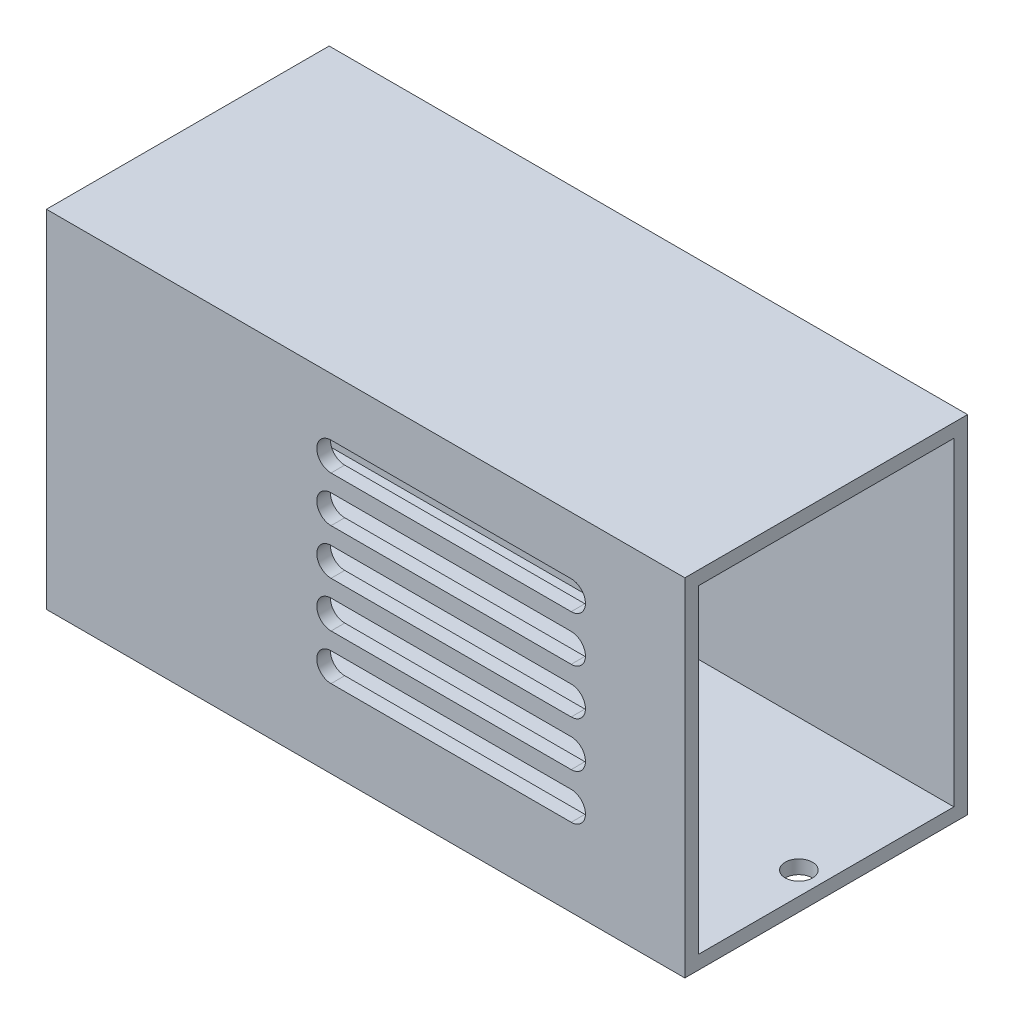
SolidWorks part; units mm, degrees
ref_plane "前视基准面" through (0, 0, 0) normal (0, 0, 1) x (1, 0, 0)
ref_plane "上视基准面" through (0, 0, 0) normal (0, 1, 0) x (1, 0, 0)
ref_plane "右视基准面" through (0, 0, 0) normal (1, 0, 0) x (0, 0, -1)
sketch "草图1" plane through (0, 0, 0) normal (0, 0, 1) x (1, 0, 0)
  line L1 (-35, 19) -> (35, 19)
  line L2 (-35, 19) -> (-35, -19)
  line L3 (-35, -19) -> (35, -19)
  line L4 (35, 19) -> (35, -19)
  line L5 (-35, 19) -> (35, -19) construction
  line L6 (-35, -19) -> (35, 19) construction
  point P0 (0, 0)
  dimension "D1" = 70
  dimension "D2" = 38
extrude "凸台-拉伸1" add sketch "草图1" along normal blind 31
sketch "草图2" plane through (35, 0, 0) normal (1, 0, 0) x (0, 0, -1)
  line L0 (-31, 0) -> (0, 0) construction
  line L1 (-31, -19) -> (-31, 19) construction
  line L3 (-29.5, 17.5) -> (-1.5, 17.5)
  line L4 (-29.5, 17.5) -> (-29.5, -17.5)
  line L5 (-29.5, -17.5) -> (-1.5, -17.5)
  line L6 (-1.5, 17.5) -> (-1.5, -17.5)
  line L7 (-29.5, 17.5) -> (-1.5, -17.5) construction
  line L8 (-29.5, -17.5) -> (-1.5, 17.5) construction
  point P5 (-15.5, 0)
  dimension "D1" = 35
  dimension "D2" = 28
extrude "切除-拉伸1" cut sketch "草图2" against normal through all
sketch "草图4" plane through (0, 0, 31) normal (0, 0, 1) x (1, 0, 0)
  line L0 (-3.7935, 11.1202) -> (22.538, 11.1202) construction
  line L1 (-3.7935, 12.6823) -> (22.538, 12.6823)
  line L2 (-3.7935, 9.5582) -> (22.538, 9.5582)
  line L3 (-3.7935, 4.5582) -> (22.538, 4.5582)
  line L4 (-3.7935, 7.6823) -> (22.538, 7.6823)
  line L5 (-3.7935, 6.1202) -> (22.538, 6.1202) construction
  line L6 (-3.7935, -0.4418) -> (22.538, -0.4418)
  line L7 (-3.7935, 2.6823) -> (22.538, 2.6823)
  line L8 (-3.7935, 1.1202) -> (22.538, 1.1202) construction
  line L9 (-3.7935, -5.4418) -> (22.538, -5.4418)
  line L10 (-3.7935, -2.3177) -> (22.538, -2.3177)
  line L11 (-3.7935, -3.8798) -> (22.538, -3.8798) construction
  line L12 (-3.7935, -10.4418) -> (22.538, -10.4418)
  line L13 (-3.7935, -7.3177) -> (22.538, -7.3177)
  line L14 (-3.7935, -8.8798) -> (22.538, -8.8798) construction
  arc A0 (-3.7935, 12.6823) -> (-3.7935, 9.5582) centre (-3.7935, 11.1202) ccw
  arc A1 (22.538, 9.5582) -> (22.538, 12.6823) centre (22.538, 11.1202) ccw
  arc A2 (-3.7935, 7.6823) -> (-3.7935, 4.5582) centre (-3.7935, 6.1202) ccw
  arc A3 (22.538, 4.5582) -> (22.538, 7.6823) centre (22.538, 6.1202) ccw
  arc A4 (-3.7935, 2.6823) -> (-3.7935, -0.4418) centre (-3.7935, 1.1202) ccw
  arc A5 (22.538, -0.4418) -> (22.538, 2.6823) centre (22.538, 1.1202) ccw
  arc A6 (-3.7935, -2.3177) -> (-3.7935, -5.4418) centre (-3.7935, -3.8798) ccw
  arc A7 (22.538, -5.4418) -> (22.538, -2.3177) centre (22.538, -3.8798) ccw
  arc A8 (-3.7935, -7.3177) -> (-3.7935, -10.4418) centre (-3.7935, -8.8798) ccw
  arc A9 (22.538, -10.4418) -> (22.538, -7.3177) centre (22.538, -8.8798) ccw
  point P2 (9.3722, 11.1202)
  point P10 (9.3722, 6.1202)
  point P17 (9.3722, 1.1202)
  point P24 (9.3722, -3.8798)
  point P31 (9.3722, -8.8798)
  dimension "D1" = 5
extrude "切除-拉伸3" cut sketch "草图4" against normal blind 2
sketch "草图5" plane through (0, -19, 0) normal (0, -1, 0) x (1, 0, 0)
  line L0 (0, 31) -> (0, 16) construction
  line L1 (-35, 31) -> (35, 31) construction
  line L2 (-32.5, 16) -> (32.5, 16) construction
  circle A0 centre (-32.5, 16) radius 1.5
  circle A1 centre (32.5, 16) radius 1.5
  point P7 (0, 16)
  dimension "D2" = 3
  dimension "D3" = 3
  dimension "D1" = 65
extrude "切除-拉伸4" cut sketch "草图5" against normal blind 2
sketch "草图6" plane through (0, -19, 0) normal (0, -1, 0) x (-1, 0, 0)
  line L0 (0, 0) -> (0, -31) construction
  line L1 (35, -31) -> (-35, -31) construction
